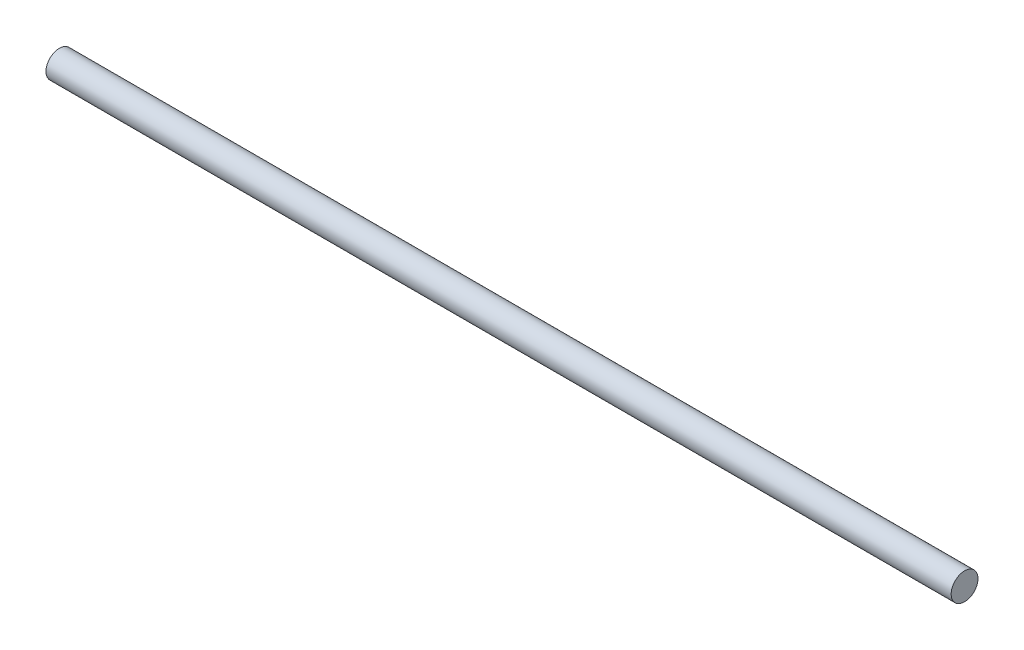
SolidWorks part; units mm, degrees
ref_plane "Спереди" through (0, 0, 0) normal (0, 0, 1) x (1, 0, 0)
ref_plane "Сверху" through (0, 0, 0) normal (0, 1, 0) x (1, 0, 0)
ref_plane "Справа" through (0, 0, 0) normal (1, 0, 0) x (0, 0, -1)
sketch "Эскиз1" plane through (0, 0, 0) normal (1, 0, 0) x (0, 0, -1)
  circle A0 centre (0, 0) radius 1.75
  dimension "D1" = 3.5
extrude "Бобышка-Вытянуть1" add sketch "Эскиз1" along normal blind 118
